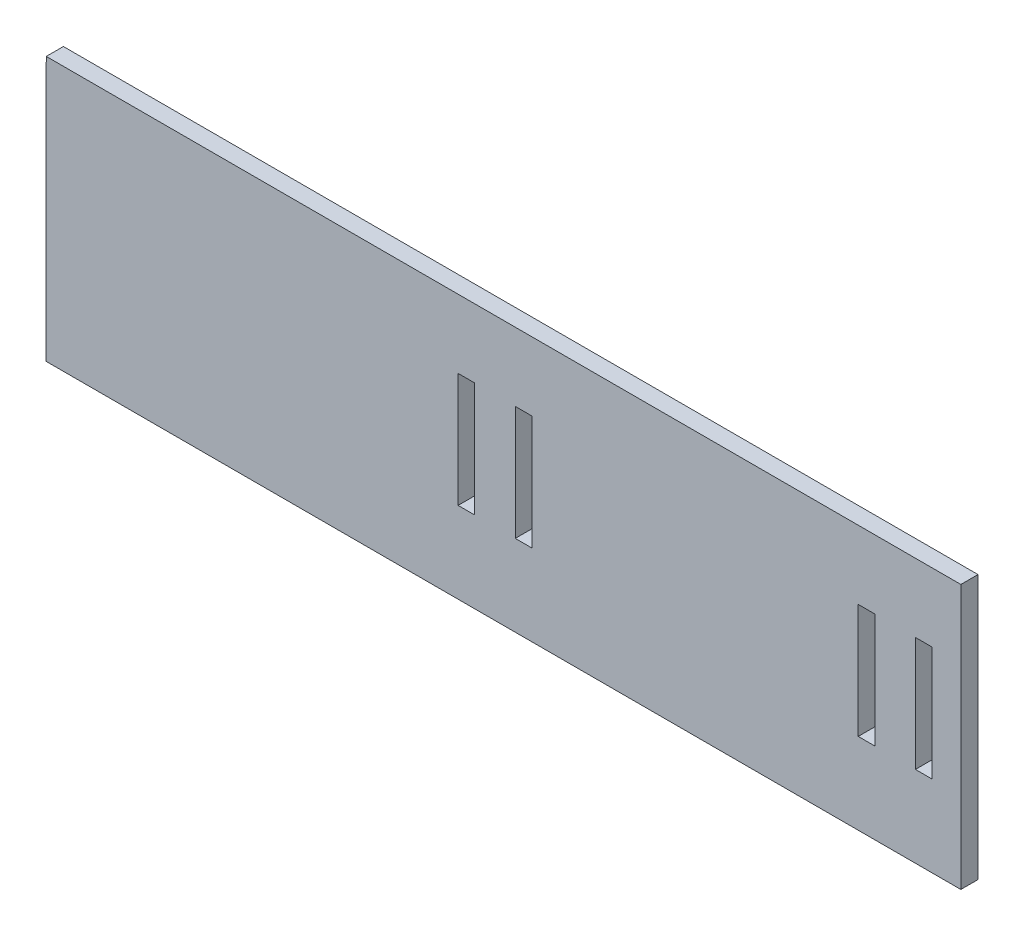
SolidWorks part; units mm, degrees
ref_plane "Front Plane" through (0, 0, 0) normal (0, 0, 1) x (1, 0, 0)
ref_plane "Top Plane" through (0, 0, 0) normal (0, 1, 0) x (1, 0, 0)
ref_plane "Right Plane" through (0, 0, 0) normal (1, 0, 0) x (0, 0, -1)
sketch "Sketch3" plane through (0, 0, 0) normal (0, 0, 1) x (1, -0.001, 0)
  line L1 (87.9077, 95.8198) -> (-72.0923, 95.6657)
  line L2 (87.9077, 95.8198) -> (87.9523, 49.6031)
  line L3 (87.9523, 49.6031) -> (-72.0923, 49.4489)
  line L4 (-72.0923, 95.6657) -> (-72.0923, 49.4489)
  line L7 (12.9078, 95.7476) -> (9.9078, 95.7447) construction
  line L8 (2.9523, 49.5212) -> (-0.0477, 49.5184) construction
  line L10 (82.9386, 63.815) -> (82.9193, 83.815) construction
  dimension "D1" = 5
  dimension "D2" = 160
extrude "Boss-Extrude1" add sketch "Sketch3" along normal blind 3
sketch "Sketch4" plane through (0, 0, 3) normal (0, 0, 1) x (1, 0, 0)
  line L0 (3, 83.7351) -> (0, 83.7351) construction
  line L1 (0.05, 83.7351) -> (2.95, 83.7351)
  line L2 (0.05, 83.7351) -> (0.05, 63.7351)
  line L3 (0.05, 63.7351) -> (2.95, 63.7351)
  line L4 (2.95, 83.7351) -> (2.95, 63.7351)
  line L5 (3, 63.7351) -> (0, 63.7351) construction
  line L6 (13, 83.7351) -> (10, 83.7351) construction
  line L7 (10.05, 83.7351) -> (12.95, 83.7351)
  line L8 (10.05, 83.7351) -> (10.05, 63.7351)
  line L9 (10.05, 63.7351) -> (12.95, 63.7351)
  line L10 (12.95, 83.7351) -> (12.95, 63.7351)
  line L11 (13, 63.7351) -> (10, 63.7351) construction
  line L12 (0, 63.7351) -> (0, 83.7351) construction
  line L13 (10, 63.7351) -> (10, 83.7351) construction
  line L14 (73, 83.7351) -> (70, 83.7351) construction
  line L15 (70.05, 83.7351) -> (72.95, 83.7351)
  line L16 (70.05, 83.7351) -> (70.05, 63.7351)
  line L17 (70.05, 63.7351) -> (72.95, 63.7351)
  line L18 (72.95, 83.7351) -> (72.95, 63.7351)
  line L19 (83, 83.7351) -> (80, 83.7351) construction
  line L20 (80.05, 83.7351) -> (82.95, 83.7351)
  line L21 (80.05, 83.7351) -> (80.05, 63.7351)
  line L22 (80.05, 63.7351) -> (82.95, 63.7351)
  line L23 (82.95, 83.7351) -> (82.95, 63.7351)
  line L24 (83, 63.7351) -> (80, 63.7351) construction
  line L25 (70, 63.7351) -> (70, 83.7351) construction
  line L26 (80, 63.7351) -> (80, 83.7351) construction
  dimension "D1" = 2.9
  dimension "D2" = 0.05
  dimension "D3" = 2.9
  dimension "D4" = 0.05
  dimension "D5" = 2.9
  dimension "D6" = 2.9
  dimension "D7" = 20
  dimension "D8" = 0.05
  dimension "D9" = 0.05
extrude "Cut-Extrude1" cut sketch "Sketch4" against normal through all
